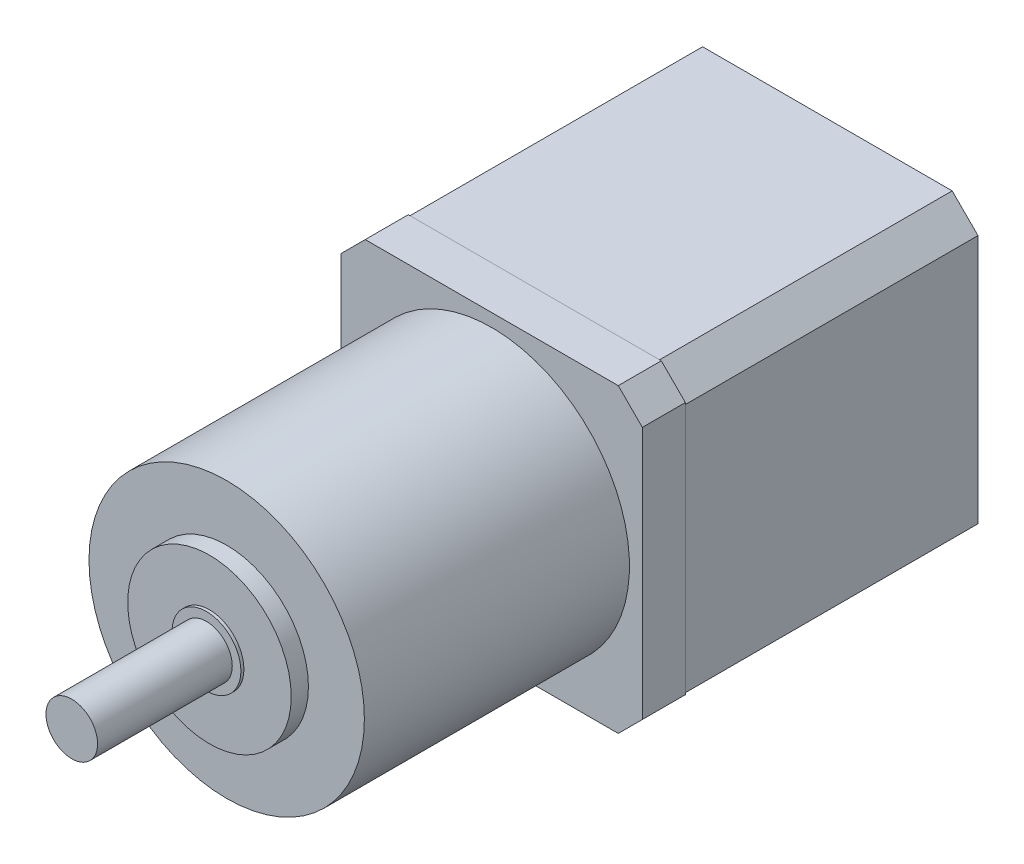
SolidWorks part; units mm, degrees
ref_plane "Front Plane" through (0, 0, 0) normal (0, 0, 1) x (1, 0, 0)
ref_plane "Top Plane" through (0, 0, 0) normal (0, 1, 0) x (1, 0, 0)
ref_plane "Right Plane" through (0, 0, 0) normal (1, 0, 0) x (0, 0, -1)
sketch "Sketch1" plane through (0, 0, 0) normal (0, 0, 1) x (1, 0, 0)
  line L1 (-17.5, 17.5) -> (17.5, 17.5)
  line L2 (-17.5, 17.5) -> (-17.5, -17.5)
  line L3 (-17.5, -17.5) -> (17.5, -17.5)
  line L4 (17.5, 17.5) -> (17.5, -17.5)
  line L5 (-17.5, 17.5) -> (17.5, -17.5) construction
  line L6 (-17.5, -17.5) -> (17.5, 17.5) construction
  point P0 (0, 0)
  dimension "D1" = 35
  dimension "D2" = 35
extrude "Boss-Extrude1" add sketch "Sketch1" along normal blind 34
chamfer "Chamfer1" distance 3 angle 45 4 edges at (-17.5, -17.5, 17) (17.5, -17.5, 17) (-17.5, 17.5, 17) (17.5, 17.5, 17)
sketch "Sketch2" plane through (0, 0, 34) normal (0, 0, 1) x (1, 0, 0)
  line L1 (-17.5, -17.5) -> (17.5, -17.5)
  line L2 (-17.5, -17.5) -> (-17.5, 17.5)
  line L3 (-17.5, 17.5) -> (17.5, 17.5)
  line L4 (17.5, -17.5) -> (17.5, 17.5)
  line L5 (-17.5, -17.5) -> (17.5, 17.5) construction
  line L6 (-17.5, 17.5) -> (17.5, -17.5) construction
  point P0 (0, 0)
  dimension "D1" = 35
  dimension "D2" = 35
extrude "Boss-Extrude2" add sketch "Sketch2" along normal blind 5 separate body
chamfer "Chamfer2" distance 2.8 angle 45 4 edges at (-17.5, -17.5, 36.5) (17.5, -17.5, 36.5) (-17.5, 17.5, 36.5) (17.5, 17.5, 36.5)
sketch "Sketch3" plane through (0, 0, 39) normal (0, 0, 1) x (1, 0, 0)
  circle A0 centre (0, 0) radius 16
  dimension "D1" = 32
extrude "Boss-Extrude3" add sketch "Sketch3" along normal blind 30.8
sketch "Sketch4" plane through (0, 0, 69.8) normal (0, 0, 1) x (1, 0, 0)
  circle A0 centre (0, 0) radius 9.5
  dimension "D1" = 19
extrude "Boss-Extrude4" add sketch "Sketch4" along normal blind 2
sketch "Sketch6" plane through (0, 0, 69.8) normal (0, 0, 1) x (1, 0, 0)
  circle A0 centre (0, 0) radius 3
  dimension "D1" = 6
extrude "Boss-Extrude5" add sketch "Sketch6" along normal blind 18
sketch "Sketch7" plane through (0, 0, 71.8) normal (0, 0, 1) x (1, 0, 0)
  circle A0 centre (0, 0) radius 4
  dimension "D1" = 8
extrude "Boss-Extrude6" add sketch "Sketch7" along normal blind 0.35
